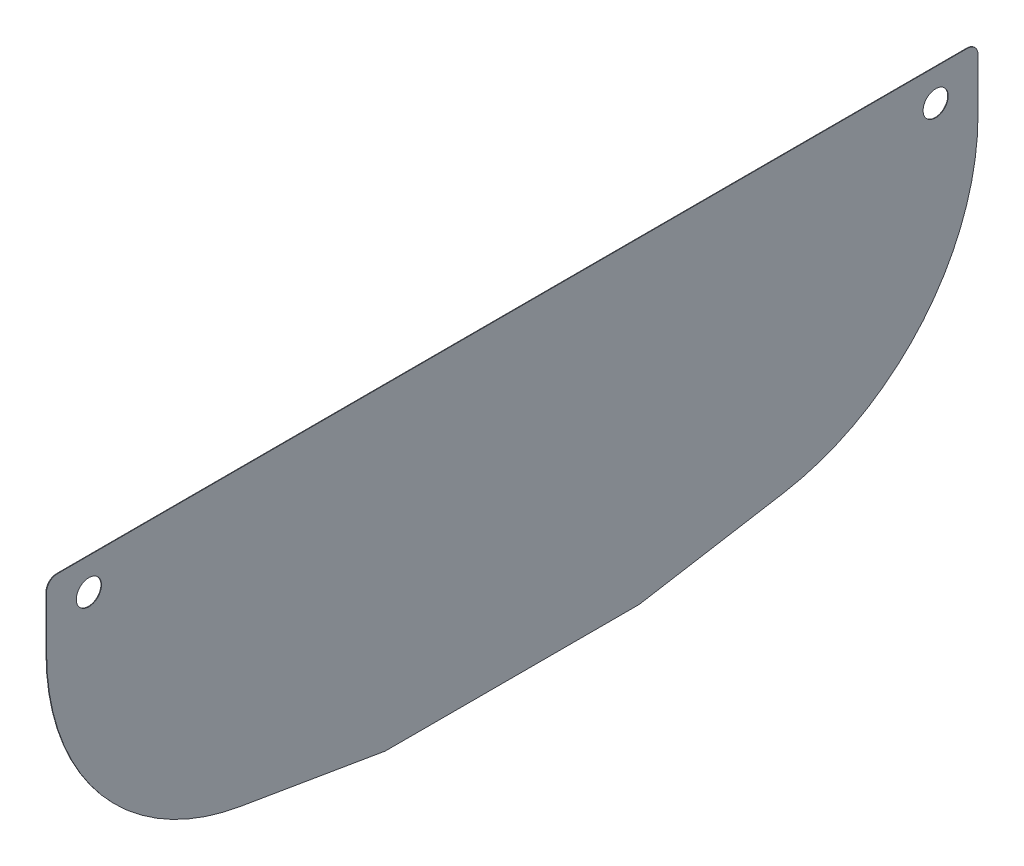
SolidWorks part; units mm, degrees
material "PC High Viscosity"
ref_plane "Front Plane" through (0, 0, 0) normal (0, 0, 1) x (1, 0, 0)
ref_plane "Top Plane" through (0, 0, 0) normal (0, 1, 0) x (1, 0, 0)
ref_plane "Right Plane" through (0, 0, 0) normal (1, 0, 0) x (0, 0, -1)
sketch "Sketch1" plane through (0, 0, 0) normal (1, 0, 0) x (0, 0, -1)
  line L2 (-558.8, 609.6) -> (-558.8, 685.8)
  line L3 (-558.8, 685.8) -> (558.8, 685.8)
  line L4 (558.8, 685.8) -> (558.8, 609.6)
  line L6 (152.4, 304.8) -> (325.92, 334.1)
  line L8 (0, 0) -> (0, 941.2231) construction
  line L9 (152.4, 304.8) -> (-152.4, 304.8)
  line L10 (-152.4, 304.8) -> (-325.92, 334.1)
  circle A0 centre (-508, 647.7) radius 15.0813
  circle A1 centre (508, 647.7) radius 15.0813
  arc A2 (325.92, 334.1) -> (558.8, 609.6) centre (279.4, 609.6) ccw
  arc A3 (-325.92, 334.1) -> (-558.8, 609.6) centre (-279.4, 609.6) cw
  dimension "D1" = 30.1625
  dimension "D11" = 609.6
  dimension "D5" = 152.4
  dimension "D2" = 1016
  dimension "D3" = 508
  dimension "D4" = 647.7
  dimension "D6" = 558.8
  dimension "D7" = 685.8
  dimension "D8" = 38.1
  dimension "D9" = 304.8
  dimension "D10" = 279.4
  dimension "D13" = 50.8
  dimension "D14" = 152.4
extrude "Boss-Extrude1" add sketch "Sketch1" along normal blind 0.635
fillet "Fillet1" radius 12.7 4 edges at (0.3175, 685.8, -558.8) (0.3175, 685.8, 558.8) (0.3175, 304.8, 152.4) (0.3175, 304.8, -152.4)
sketch "Sketch4" plane through (0.635, 0, 0) normal (1, 0, 0) x (0, 0, -1)
  arc A0 (-500.9147, 634.3868) -> (500.9147, 634.3868) centre (0, 909.5172) ccw construction
  circle A1 centre (-508, 647.7) radius 15.0812 construction
  circle A2 centre (508, 647.7) radius 15.0813 construction
  circle A3 centre (-508, 647.7) radius 15.0813 construction
  circle A4 centre (508, 647.7) radius 15.0813 construction
  circle A5 centre (0, 345.9547) radius 3.3655
  circle A6 centre (0, 330.0797) radius 3.3655
  point P12 (0, 338.0172)
  dimension "D1" = 571.5
  dimension "D2" = 6.731
  dimension "D3" = 15.875
  dimension "D4" = 7.9375
